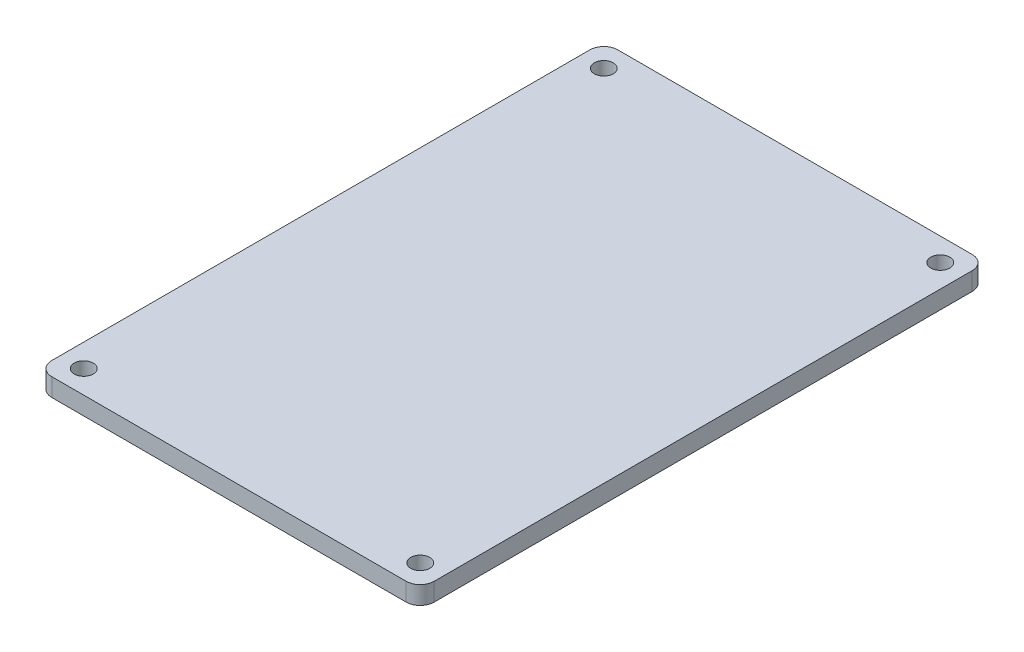
SolidWorks part; units mm, degrees
ref_plane "Front" through (0, 0, 0) normal (0, 0, 1) x (1, 0, 0)
ref_plane "Top" through (0, 0, 0) normal (0, 1, 0) x (1, 0, 0)
ref_plane "Right" through (0, 0, 0) normal (1, 0, 0) x (0, 0, -1)
sketch "Sketch1" plane through (0, 0, 0) normal (0, 1, 0) x (1, 0, 0)
  line L1 (-29.43, -47) -> (29.43, -47)
  line L2 (-31.75, -44.68) -> (-31.75, 44.68)
  line L3 (-29.43, 47) -> (29.43, 47)
  line L4 (31.75, -44.68) -> (31.75, 44.68)
  line L5 (-31.75, -47) -> (31.75, 47) construction
  line L6 (-31.75, 47) -> (31.75, -47) construction
  arc A0 (-29.43, -47) -> (-31.75, -44.68) centre (-29.43, -44.68) cw
  arc A1 (29.43, -47) -> (31.75, -44.68) centre (29.43, -44.68) ccw
  arc A2 (29.43, 47) -> (31.75, 44.68) centre (29.43, 44.68) cw
  arc A3 (-29.43, 47) -> (-31.75, 44.68) centre (-29.43, 44.68) ccw
  point P0 (0, 0)
  dimension "D3" = 2.32
  dimension "D1" = 94
  dimension "D2" = 63.5
extrude "Boss-Extrude1" add sketch "Sketch1" along normal blind 3
sketch "Sketch2" plane through (0, 3, 0) normal (0, 1, 0) x (1, 0, 0)
  point P0 (-27.94, 43.18)
  point P1 (27.94, 43.18)
  point P2 (27.94, -43.18)
  point P3 (-27.94, -43.18)
  point P5 (0, 0)
  point P6 (0, 0)
  point P7 (0, 0)
  point P8 (0, 0)
  point P9 (0, 0)
  point P10 (-28.5115, -43.18)
  point P11 (0, 0)
  point P12 (0, 0)
  point P13 (0, 0)
  point P14 (-28.94, 43.18)
  dimension "D1" = 86.36
  dimension "D2" = 43.18
  dimension "D3" = 27.94
  dimension "D4" = 55.88
hole_wizard "Ø1.0mm Dowel Hole1" positions "Sketch4" profile "Sketch5" hole size "Ø1.0" standard "ANSI Metric" end condition through all
sketch "Sketch4" plane through (0, 3, 0) normal (0, 1, 0) x (1, 0, 0)
  point P0 (27.94, 43.18)
  point P3 (-27.94, 43.18)
  point P6 (-27.94, -43.18)
  point P9 (27.94, -43.18)
sketch "Sketch5" plane through (27.94, 3, -43.18) normal (1, 0, 0) x (0, 0, 1)
  line L0 (0, 0) -> (0, 3)
  line L1 (0, 3) -> (1.58, 3)
  line L2 (1.58, 3) -> (1.58, 0)
  line L5 (1.58, 0) -> (0, 0)
  line L11 (0, -6.35) -> (0, 107.95) construction
  dimension "Thru Hole Dia." = 3.16
  dimension "Thru Hole Depth" = 3
